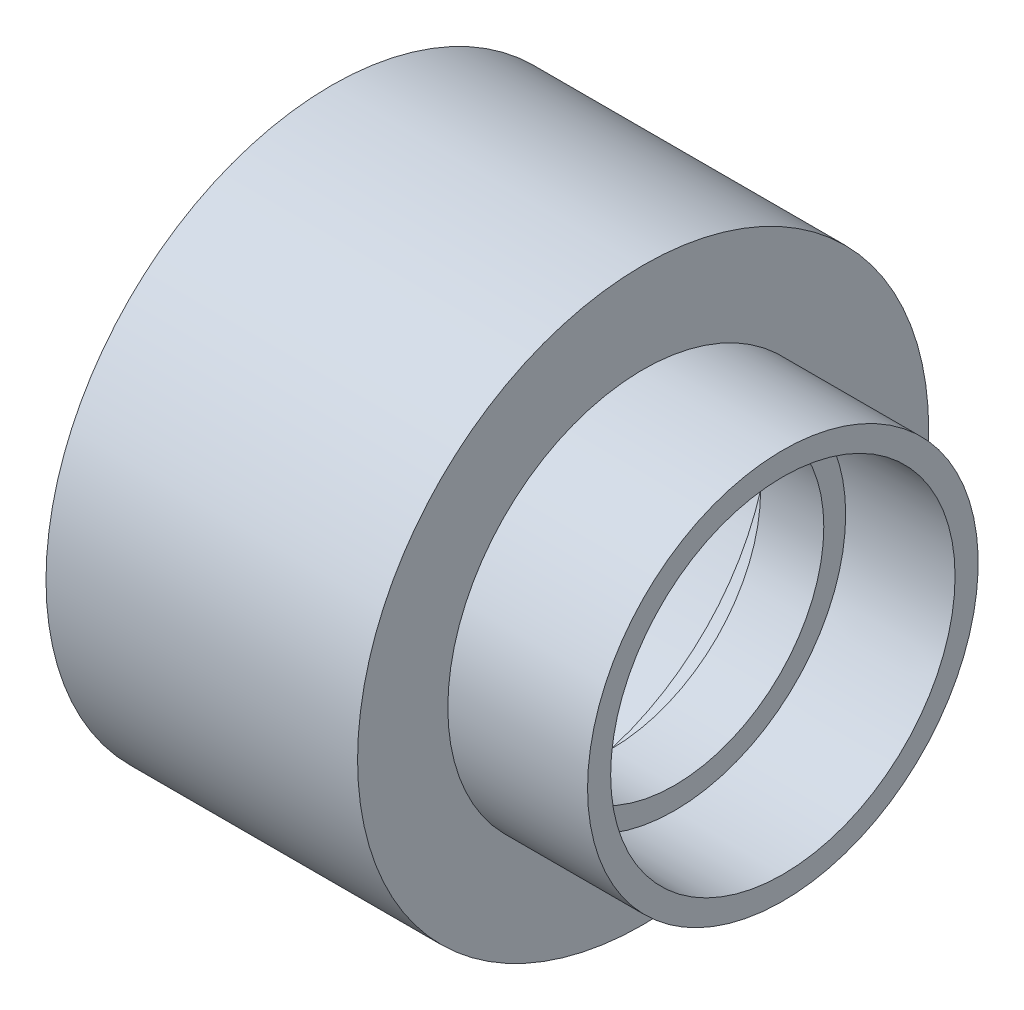
SolidWorks part; units mm, degrees
ref_plane "Front Plane" through (0, 0, 0) normal (0, 0, 1) x (1, 0, 0)
ref_plane "Top Plane" through (0, 0, 0) normal (0, 1, 0) x (1, 0, 0)
ref_plane "Right Plane" through (0, 0, 0) normal (1, 0, 0) x (0, 0, -1)
sketch "Sketch0" plane through (0, 0, 0) normal (0, 0, 1) x (1, 0, 0)
  line L0 (-49.2125, 0) -> (0, 0) construction
  line L1 (0, 0) -> (0, 50.2285) construction
  line L2 (-11.1125, 0) -> (11.1125, 0) construction
  line L3 (0, 0) -> (30.1625, 0) construction
  line L4 (-49.2125, 50.2285) -> (-49.2125, -50.2285) construction
  line L5 (-11.1125, 44.3865) -> (-49.2125, 44.6405) construction
  line L6 (-11.1125, 44.3865) -> (-11.1125, -44.3865) construction
  line L7 (-11.1125, -44.3865) -> (-49.2125, -44.6405) construction
  line L8 (-49.2125, 44.6405) -> (-49.2125, -44.6405) construction
  line L9 (30.1625, 0) -> (11.1125, 0) construction
  line L10 (11.1125, 30.099) -> (11.1125, -30.099) construction
  line L11 (11.1125, 26.2509) -> (11.1125, -26.2509) construction
  line L12 (30.1625, 34.3535) -> (30.1625, -34.3535) construction
  line L13 (30.1625, 30.2895) -> (30.1625, -30.2895) construction
  line L14 (-11.1125, 38.9636) -> (-11.1125, -38.9636) construction
  line L15 (-11.1125, -38.9636) -> (-11.1125, -44.5516) construction
  line L16 (-49.2125, -44.6405) -> (-49.2125, -50.2285) construction
  line L17 (30.1625, -30.2895) -> (11.1125, -30.099) construction
  line L21 (-49.2125, 0) -> (-11.1125, 0) construction
  dimension "A" = 22.225
  dimension "OD A 1" = 89.281
  dimension "OD B 1" = 88.773
  dimension "ID 1" = 77.9272
  dimension "H 1" = 5.588
  dimension "C 1" = 38.1
  dimension "OD A 2" = 60.579
  dimension "OD B 2" = 60.198
  dimension "ID 2" = 52.5018
  dimension "C 2" = 19.05
  dimension "H 2" = 4.064
sketch "Sketch1" plane through (0, 0, 0) normal (0, 0, 1) x (1, 0, 0)
  line L0 (-49.2125, 0) -> (0, 0) construction
  line L1 (-49.2125, 0) -> (0, 0) construction
  line L2 (-49.2125, -50.2285) -> (5.588, -50.2285)
  line L3 (0, 0) -> (0, -50.2285) construction
  line L4 (-49.2125, -50.2285) -> (-49.2125, -44.6405)
  line L5 (-49.2125, -44.6405) -> (-11.1125, -44.3865)
  line L6 (30.1625, -34.3535) -> (5.588, -34.3535)
  line L7 (30.1625, -34.3535) -> (30.1625, -30.2895)
  line L8 (-11.1125, -38.9636) -> (-11.1125, -44.3865)
  line L9 (30.1625, -30.2895) -> (11.1125, -30.099)
  line L10 (11.1125, -30.099) -> (11.1125, -26.2509)
  line L11 (-11.1125, -38.9636) -> (0, -38.9636)
  line L12 (11.1125, -26.2509) -> (0, -26.2509)
  line L13 (0, -26.2509) -> (0, -38.9636)
  line L14 (5.588, -34.3535) -> (5.588, -50.2285)
  line L15 (5.588, -26.2509) -> (5.588, -34.3535) construction
  line L16 (5.588, -34.3535) -> (0, -34.3535) construction
revolve "Revolve1" add sketch "Sketch1" angle 360 about L1
